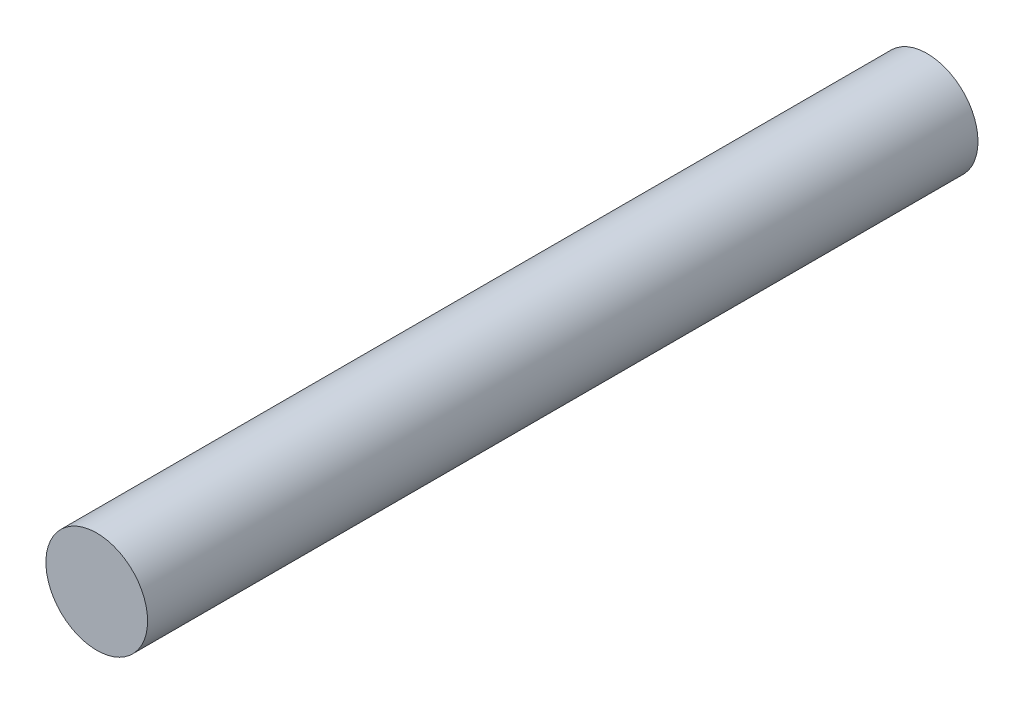
SolidWorks part; units mm, degrees
ref_plane "Plan de face" through (0, 0, 0) normal (0, 0, 1) x (1, 0, 0)
ref_plane "Plan de dessus" through (0, 0, 0) normal (0, 1, 0) x (1, 0, 0)
ref_plane "Plan de droite" through (0, 0, 0) normal (1, 0, 0) x (0, 0, -1)
sketch "Esquisse1" plane through (0, 0, 0) normal (0, 0, 1) x (1, 0, 0)
  circle A0 centre (0, 0) radius 3
extrude "Extrusion1" add sketch "Esquisse1" along normal blind 49
